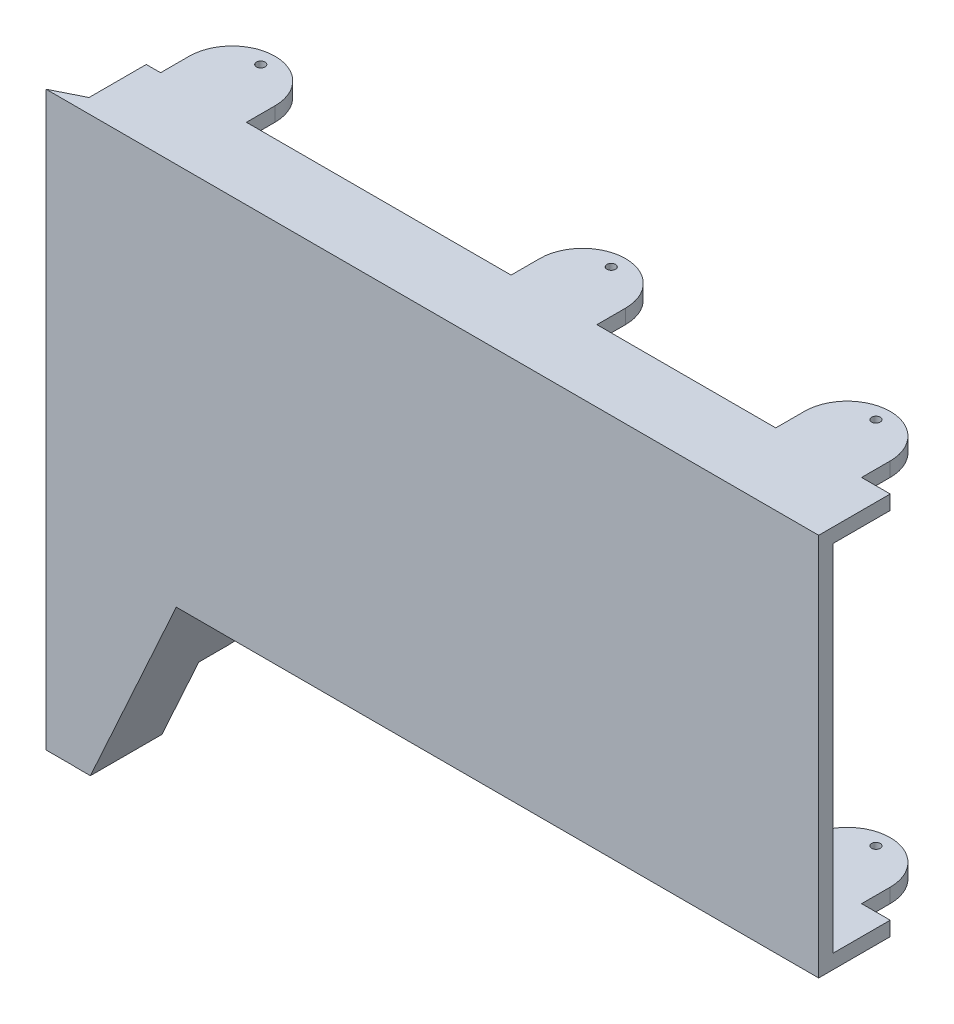
SolidWorks part; units mm, degrees
ref_plane "Front Plane" through (0, 0, 0) normal (0, 0, 1) x (1, 0, 0)
ref_plane "Top Plane" through (0, 0, 0) normal (0, 1, 0) x (1, 0, 0)
ref_plane "Right Plane" through (0, 0, 0) normal (1, 0, 0) x (0, 0, -1)
sketch "Sketch1" plane through (0, 0, 0) normal (0, 0, 1) x (1, 0, 0)
  line L1 (0, 0) -> (260, 0)
  line L2 (0, 0) -> (0, -134)
  line L3 (0, -134) -> (260, -134)
  line L4 (260, 0) -> (260, -134)
  dimension "D1" = 134
  dimension "D2" = 260
extrude "Boss-Extrude1" add sketch "Sketch1" along normal blind 5
sketch "Sketch2" plane through (0, 0, 0) normal (0, 0, -1) x (-1, 0, 0)
  line L0 (-260, 0) -> (0, 0) construction
  line L1 (-260, 0) -> (0, 0)
  line L2 (-260, 0) -> (-260, -5)
  line L3 (-260, -5) -> (0, -5)
  line L4 (0, 0) -> (0, -5)
  line L5 (-260, -134) -> (-260, 0) construction
  line L6 (0, 0) -> (0, -134) construction
  dimension "D1" = 5
extrude "Boss-Extrude2" add sketch "Sketch2" along normal blind 20
sketch "Sketch4" plane through (0, 0, 0) normal (0, 0, -1) x (-1, 0, 0)
  line L1 (-260, -129) -> (-30, -129)
  line L2 (-260, -129) -> (-260, -134)
  line L3 (-260, -134) -> (-30, -134)
  line L4 (-30, -129) -> (-30, -134)
  line L5 (0, -134) -> (-260, -134) construction
  line L7 (-260, -134) -> (-260, -5) construction
  line L8 (0, -5) -> (0, -134) construction
  dimension "D1" = 5
  dimension "D2" = 30
extrude "Boss-Extrude3" add sketch "Sketch4" along normal blind 20
sketch "Sketch6" plane through (0, 0, 0) normal (0, 1, 0) x (1, 0, 0)
  line L0 (0, -5) -> (0, 20) construction
  line L1 (5, 20) -> (5, 30)
  line L2 (35, 20) -> (35, 30)
  line L4 (0, 20) -> (260, 20) construction
  line L5 (35, 20) -> (5, 20)
  arc A0 (35, 30) -> (5, 30) centre (20, 30) ccw
  dimension "D4" = 15
  dimension "D1" = 5
  dimension "D2" = 30
  dimension "D3" = 10
extrude "Boss-Extrude4" add sketch "Sketch6" against normal blind 5
sketch "Sketch7" plane through (0, 0, 0) normal (0, 1, 0) x (1, 0, 0)
  line L0 (20, 45) -> (20, 40) construction
  line L1 (5, 30) -> (5, 20) construction
  line L2 (35, 20) -> (35, 30) construction
  circle A0 centre (20, 40) radius 1.5
  arc A2 (35, 30) -> (5, 30) centre (20, 30) ccw construction
  point P4 (0, 0)
  point P5 (0, 0)
  dimension "D1" = 3
  dimension "D2" = 5
extrude "Cut-Extrude1" cut sketch "Sketch7" against normal blind 5
sketch "Sketch8" plane through (0, 0, 0) normal (0, 0, -1) x (-1, 0, 0)
  line L0 (-30, -134) -> (0, -200)
  line L1 (0, -200) -> (0, -134)
  line L2 (0, -134) -> (-30, -134)
  line L3 (0, -134) -> (-30, -134) construction
  line L4 (0, -5) -> (0, -134) construction
  dimension "D1" = 200
extrude "Boss-Extrude5" add sketch "Sketch8" against normal blind 5
sketch "Sketch10" plane through (0, 0, 5) normal (0, 0, 1) x (1, 0, 0)
  line L0 (30, -134) -> (35.4923, -134)
  line L1 (30, -134) -> (-0.0225, -200.0494)
  line L2 (-0.0225, -200.0494) -> (5.4698, -200.0494)
  line L3 (35.4923, -134) -> (5.4698, -200.0494)
  line L5 (30, -134) -> (0, -200) construction
  line L6 (30, -134) -> (260, -134) construction
  dimension "D1" = 5
extrude "Boss-Extrude9" add sketch "Sketch10" against normal blind 25
sketch "Sketch11" plane through (0, 0, 0) normal (0, 1, 0) x (1, 0, 0)
  line L0 (0, 0) -> (-10, -5)
  line L1 (-10, -5) -> (0, -5)
  line L2 (0, -5) -> (0, 0)
  line L3 (0, -5) -> (0, 20) construction
  line L4 (260, -5) -> (0, -5) construction
  dimension "D1" = 5
  dimension "D2" = 10
extrude "Boss-Extrude10" add sketch "Sketch11" against normal blind 200
sketch "Sketch13" plane through (0, 0, 0) normal (0, 1, 0) x (1, 0, 0)
  line L0 (35, 20) -> (260, 20) construction
  line L2 (220, 30) -> (220, 20)
  line L5 (220, 20) -> (250, 20)
  line L6 (250, 30) -> (250, 20)
  line L7 (260, -5) -> (260, 20) construction
  arc A0 (250, 30) -> (220, 30) centre (235, 30) ccw
  dimension "D3" = 15
  dimension "D1" = 10
  dimension "D2" = 30
  dimension "D4" = 10
extrude "Boss-Extrude11" add sketch "Sketch13" against normal blind 5
sketch "Sketch14" plane through (0, 0, 0) normal (0, 1, 0) x (1, 0, 0)
  line L0 (235, 45) -> (235, 40) construction
  line L1 (220, 30) -> (220, 20) construction
  line L2 (250, 20) -> (250, 30) construction
  circle A0 centre (235, 40) radius 1.5
  arc A2 (250, 30) -> (220, 30) centre (235, 30) ccw construction
  dimension "D1" = 3
  dimension "D2" = 5
extrude "Cut-Extrude2" cut sketch "Sketch14" against normal blind 5
ref_plane "Plane1" through (0, -67, 0) normal (0, 1, 0) x (1, 0, 0)
sketch "Sketch15" plane through (0, 0, -20) normal (0, 0, -1) x (-1, 0, 0)
  line L0 (-35, -5) -> (-5, -5) construction
  line L1 (-30.7589, -144.4135) -> (-26.207, -142.3445)
  line L2 (-30.7589, -144.4135) -> (-18.3448, -171.7245)
  line L3 (-18.3448, -171.7245) -> (-13.793, -169.6555)
  line L4 (-26.207, -142.3445) -> (-13.793, -169.6555)
  line L5 (-30, -134) -> (0, -200) construction
  line L6 (-5.4698, -200.0494) -> (-35.4923, -134) construction
  line L7 (-20, -156) -> (-20, -5) construction
  point P4 (-20, -156)
  point P9 (-20, -5)
  point P14 (0, 0)
  point P15 (-14.424, -162.4977)
  point P16 (0, 0)
  dimension "D1" = 30
extrude "Boss-Extrude12" add sketch "Sketch15" along normal blind 10
sketch "Sketch17" plane through (75.3425, -34.2466, 0) normal (-0.9104, 0.4138, 0) x (0, 0, 1)
  line L0 (-30, -118.7411) -> (-30, -148.7411)
  line L1 (-30, -148.7411) -> (-30, -118.7411) construction
  arc A1 (-30, -118.7411) -> (-30, -148.7411) centre (-30, -133.7411) ccw
  point P4 (0, 0)
  point P5 (0, 0)
  point P7 (0, 0)
  point P9 (0, 0)
  point P10 (-25, -141.8702)
  point P11 (0, 0)
  point P13 (0, 0)
extrude "Boss-Extrude13" add sketch "Sketch17" against normal blind 5
ref_plane "Plane2" through (0, -155, 0) normal (0, 1, 0) x (1, 0, 0)
sketch "Sketch19" plane through (0, -155, 0) normal (0, 1, 0) x (1, 0, 0)
  circle A0 centre (20, 40) radius 1.5
  circle A1 centre (20, 40) radius 1.5 construction
  dimension "D1" = 3
extrude "Cut-Extrude4" cut sketch "Sketch19" against normal through all both and the other way through all
ref_plane "Plane4" through (188.75, 0, 0) normal (-1, 0, 0) x (0, 0, 1)
mirror "Mirror4" about plane through (0, -67, 0) normal (0, 1, 0) of "Cut-Extrude2", "Boss-Extrude11" second plane through (188.75, 0, 0) second plane normal (-1, 0, 0)
